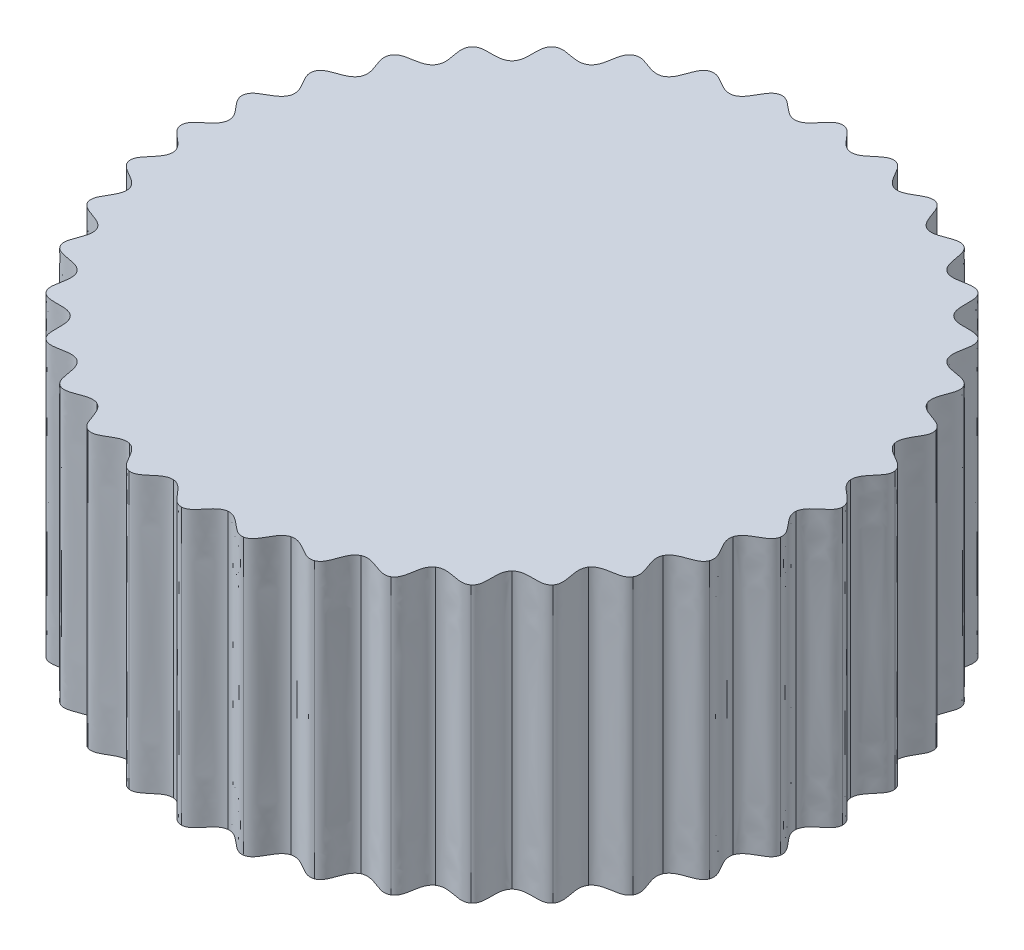
SolidWorks part; units mm, degrees
ref_plane "Front Plane" through (0, 0, 0) normal (0, 0, 1) x (1, 0, 0)
ref_plane "Top Plane" through (0, 0, 0) normal (0, 1, 0) x (1, 0, 0)
ref_plane "Right Plane" through (0, 0, 0) normal (1, 0, 0) x (0, 0, -1)
sketch "Sketch1" plane through (0, 0, 0) normal (0, 1, 0) x (1, 0, 0)
  line L0 (0, 0) -> (0, 36) construction
  line L1 (0, 0) -> (3.1376, 35.863) construction
  line L2 (-0.5, 36) -> (0.5, 36) construction
  line L4 (0, 36) -> (2.9633, 33.8706) construction
  circle A1 centre (0, 0) radius 36 construction
  circle A2 centre (0, 0) radius 34 construction
  spline S0 degree 3 poles (0, 36) (0.6252, 36.0076) (1.4819, 34.8993) (2.3376, 33.935) (2.9633, 33.8706) knots 0 0 0 0 0.5 1 1 1 1
  spline S1 degree 3 poles (0, 36) (-0.6252, 36.0076) (-1.4819, 34.8993) (-2.3376, 33.935) (-2.9633, 33.8706) knots 0 0 0 0 0.5 1 1 1 1
  spline S2 degree 3 poles (6.2513, 35.4531) (5.6369, 35.5691) (4.6008, 34.6264) (3.5907, 33.8254) (2.9633, 33.8706) knots 0 0 0 0 0.5 1 1 1 1
  spline S3 degree 3 poles (6.2513, 35.4531) (6.8684, 35.3519) (7.5196, 34.1118) (8.1948, 33.0136) (8.7998, 32.8415) knots 0 0 0 0 0.5 1 1 1 1
  spline S4 degree 3 poles (12.3127, 33.8289) (11.7278, 34.0499) (10.5438, 33.3015) (9.4099, 32.688) (8.7998, 32.8415) knots 0 0 0 0 0.5 1 1 1 1
  spline S5 degree 3 poles (12.3127, 33.8289) (12.9028, 33.6222) (13.3288, 32.2878) (13.8031, 31.089) (14.369, 30.8145) knots 0 0 0 0 0.5 1 1 1 1
  spline S6 degree 3 poles (18, 31.1769) (17.4623, 31.4961) (16.1663, 30.9646) (14.9431, 30.5574) (14.369, 30.8145) knots 0 0 0 0 0.5 1 1 1 1
  spline S7 degree 3 poles (18, 31.1769) (18.5452, 30.8708) (18.733, 29.4828) (18.9919, 28.2198) (19.5016, 27.8512) knots 0 0 0 0 0.5 1 1 1 1
  spline S8 degree 3 poles (23.1404, 27.5776) (22.6663, 27.9853) (21.2977, 27.687) (20.0223, 27.4983) (19.5016, 27.8512) knots 0 0 0 0 0.5 1 1 1 1
  spline S9 degree 3 poles (23.1404, 27.5776) (23.6242, 27.1815) (23.568, 25.7819) (23.6037, 24.4932) (24.0416, 24.0416) knots 0 0 0 0 0.5 1 1 1 1
  spline S10 degree 3 poles (27.5776, 23.1404) (27.1815, 23.6242) (25.7819, 23.568) (24.4932, 23.6037) (24.0416, 24.0416) knots 0 0 0 0 0.5 1 1 1 1
  spline S11 degree 3 poles (27.5776, 23.1404) (27.9853, 22.6663) (27.687, 21.2977) (27.4983, 20.0223) (27.8512, 19.5016) knots 0 0 0 0 0.5 1 1 1 1
  spline S12 degree 3 poles (31.1769, 18) (30.8708, 18.5452) (29.4828, 18.733) (28.2198, 18.9919) (27.8512, 19.5016) knots 0 0 0 0 0.5 1 1 1 1
  spline S13 degree 3 poles (31.1769, 18) (31.4961, 17.4623) (30.9646, 16.1663) (30.5574, 14.9431) (30.8145, 14.369) knots 0 0 0 0 0.5 1 1 1 1
  spline S14 degree 3 poles (33.8289, 12.3127) (33.6222, 12.9028) (32.2878, 13.3288) (31.089, 13.8031) (30.8145, 14.369) knots 0 0 0 0 0.5 1 1 1 1
  spline S15 degree 3 poles (33.8289, 12.3127) (34.0499, 11.7278) (33.3015, 10.5438) (32.688, 9.4099) (32.8415, 8.7998) knots 0 0 0 0 0.5 1 1 1 1
  spline S16 degree 3 poles (35.4531, 6.2513) (35.3519, 6.8684) (34.1118, 7.5196) (33.0136, 8.1948) (32.8415, 8.7998) knots 0 0 0 0 0.5 1 1 1 1
  spline S17 degree 3 poles (35.4531, 6.2513) (35.5691, 5.6369) (34.6264, 4.6008) (33.8254, 3.5907) (33.8706, 2.9633) knots 0 0 0 0 0.5 1 1 1 1
  spline S18 degree 3 poles (36, 0) (36.0076, 0.6252) (34.8993, 1.4819) (33.935, 2.3376) (33.8706, 2.9633) knots 0 0 0 0 0.5 1 1 1 1
  spline S19 degree 3 poles (36, 0) (36.0076, -0.6252) (34.8993, -1.4819) (33.935, -2.3376) (33.8706, -2.9633) knots 0 0 0 0 0.5 1 1 1 1
  spline S20 degree 3 poles (35.4531, -6.2513) (35.5691, -5.6369) (34.6264, -4.6008) (33.8254, -3.5907) (33.8706, -2.9633) knots 0 0 0 0 0.5 1 1 1 1
  spline S21 degree 3 poles (35.4531, -6.2513) (35.3519, -6.8684) (34.1118, -7.5196) (33.0136, -8.1948) (32.8415, -8.7998) knots 0 0 0 0 0.5 1 1 1 1
  spline S22 degree 3 poles (33.8289, -12.3127) (34.0499, -11.7278) (33.3015, -10.5438) (32.688, -9.4099) (32.8415, -8.7998) knots 0 0 0 0 0.5 1 1 1 1
  spline S23 degree 3 poles (33.8289, -12.3127) (33.6222, -12.9028) (32.2878, -13.3288) (31.089, -13.8031) (30.8145, -14.369) knots 0 0 0 0 0.5 1 1 1 1
  spline S24 degree 3 poles (31.1769, -18) (31.4961, -17.4623) (30.9646, -16.1663) (30.5574, -14.9431) (30.8145, -14.369) knots 0 0 0 0 0.5 1 1 1 1
  spline S25 degree 3 poles (31.1769, -18) (30.8708, -18.5452) (29.4828, -18.733) (28.2198, -18.9919) (27.8512, -19.5016) knots 0 0 0 0 0.5 1 1 1 1
  spline S26 degree 3 poles (27.5776, -23.1404) (27.9853, -22.6663) (27.687, -21.2977) (27.4983, -20.0223) (27.8512, -19.5016) knots 0 0 0 0 0.5 1 1 1 1
  spline S27 degree 3 poles (27.5776, -23.1404) (27.1815, -23.6242) (25.7819, -23.568) (24.4932, -23.6037) (24.0416, -24.0416) knots 0 0 0 0 0.5 1 1 1 1
  spline S28 degree 3 poles (23.1404, -27.5776) (23.6242, -27.1815) (23.568, -25.7819) (23.6037, -24.4932) (24.0416, -24.0416) knots 0 0 0 0 0.5 1 1 1 1
  spline S29 degree 3 poles (23.1404, -27.5776) (22.6663, -27.9853) (21.2977, -27.687) (20.0223, -27.4983) (19.5016, -27.8512) knots 0 0 0 0 0.5 1 1 1 1
  spline S30 degree 3 poles (18, -31.1769) (18.5452, -30.8708) (18.733, -29.4828) (18.9919, -28.2198) (19.5016, -27.8512) knots 0 0 0 0 0.5 1 1 1 1
  spline S31 degree 3 poles (18, -31.1769) (17.4623, -31.4961) (16.1663, -30.9646) (14.9431, -30.5574) (14.369, -30.8145) knots 0 0 0 0 0.5 1 1 1 1
  spline S32 degree 3 poles (12.3127, -33.8289) (12.9028, -33.6222) (13.3288, -32.2878) (13.8031, -31.089) (14.369, -30.8145) knots 0 0 0 0 0.5 1 1 1 1
  spline S33 degree 3 poles (12.3127, -33.8289) (11.7278, -34.0499) (10.5438, -33.3015) (9.4099, -32.688) (8.7998, -32.8415) knots 0 0 0 0 0.5 1 1 1 1
  spline S34 degree 3 poles (6.2513, -35.4531) (6.8684, -35.3519) (7.5196, -34.1118) (8.1948, -33.0136) (8.7998, -32.8415) knots 0 0 0 0 0.5 1 1 1 1
  spline S35 degree 3 poles (6.2513, -35.4531) (5.6369, -35.5691) (4.6008, -34.6264) (3.5907, -33.8254) (2.9633, -33.8706) knots 0 0 0 0 0.5 1 1 1 1
  spline S36 degree 3 poles (0, -36) (0.6252, -36.0076) (1.4819, -34.8993) (2.3376, -33.935) (2.9633, -33.8706) knots 0 0 0 0 0.5 1 1 1 1
  spline S37 degree 3 poles (0, -36) (-0.6252, -36.0076) (-1.4819, -34.8993) (-2.3376, -33.935) (-2.9633, -33.8706) knots 0 0 0 0 0.5 1 1 1 1
  spline S38 degree 3 poles (-6.2513, -35.4531) (-5.6369, -35.5691) (-4.6008, -34.6264) (-3.5907, -33.8254) (-2.9633, -33.8706) knots 0 0 0 0 0.5 1 1 1 1
  spline S39 degree 3 poles (-6.2513, -35.4531) (-6.8684, -35.3519) (-7.5196, -34.1118) (-8.1948, -33.0136) (-8.7998, -32.8415) knots 0 0 0 0 0.5 1 1 1 1
  spline S40 degree 3 poles (-12.3127, -33.8289) (-11.7278, -34.0499) (-10.5438, -33.3015) (-9.4099, -32.688) (-8.7998, -32.8415) knots 0 0 0 0 0.5 1 1 1 1
  spline S41 degree 3 poles (-12.3127, -33.8289) (-12.9028, -33.6222) (-13.3288, -32.2878) (-13.8031, -31.089) (-14.369, -30.8145) knots 0 0 0 0 0.5 1 1 1 1
  spline S42 degree 3 poles (-18, -31.1769) (-17.4623, -31.4961) (-16.1663, -30.9646) (-14.9431, -30.5574) (-14.369, -30.8145) knots 0 0 0 0 0.5 1 1 1 1
  spline S43 degree 3 poles (-18, -31.1769) (-18.5452, -30.8708) (-18.733, -29.4828) (-18.9919, -28.2198) (-19.5016, -27.8512) knots 0 0 0 0 0.5 1 1 1 1
  spline S44 degree 3 poles (-23.1404, -27.5776) (-22.6663, -27.9853) (-21.2977, -27.687) (-20.0223, -27.4983) (-19.5016, -27.8512) knots 0 0 0 0 0.5 1 1 1 1
  spline S45 degree 3 poles (-23.1404, -27.5776) (-23.6242, -27.1815) (-23.568, -25.7819) (-23.6037, -24.4932) (-24.0416, -24.0416) knots 0 0 0 0 0.5 1 1 1 1
  spline S46 degree 3 poles (-27.5776, -23.1404) (-27.1815, -23.6242) (-25.7819, -23.568) (-24.4932, -23.6037) (-24.0416, -24.0416) knots 0 0 0 0 0.5 1 1 1 1
  spline S47 degree 3 poles (-27.5776, -23.1404) (-27.9853, -22.6663) (-27.687, -21.2977) (-27.4983, -20.0223) (-27.8512, -19.5016) knots 0 0 0 0 0.5 1 1 1 1
  spline S48 degree 3 poles (-31.1769, -18) (-30.8708, -18.5452) (-29.4828, -18.733) (-28.2198, -18.9919) (-27.8512, -19.5016) knots 0 0 0 0 0.5 1 1 1 1
  spline S49 degree 3 poles (-31.1769, -18) (-31.4961, -17.4623) (-30.9646, -16.1663) (-30.5574, -14.9431) (-30.8145, -14.369) knots 0 0 0 0 0.5 1 1 1 1
  spline S50 degree 3 poles (-33.8289, -12.3127) (-33.6222, -12.9028) (-32.2878, -13.3288) (-31.089, -13.8031) (-30.8145, -14.369) knots 0 0 0 0 0.5 1 1 1 1
  spline S51 degree 3 poles (-33.8289, -12.3127) (-34.0499, -11.7278) (-33.3015, -10.5438) (-32.688, -9.4099) (-32.8415, -8.7998) knots 0 0 0 0 0.5 1 1 1 1
  spline S52 degree 3 poles (-35.4531, -6.2513) (-35.3519, -6.8684) (-34.1118, -7.5196) (-33.0136, -8.1948) (-32.8415, -8.7998) knots 0 0 0 0 0.5 1 1 1 1
  spline S53 degree 3 poles (-35.4531, -6.2513) (-35.5691, -5.6369) (-34.6264, -4.6008) (-33.8254, -3.5907) (-33.8706, -2.9633) knots 0 0 0 0 0.5 1 1 1 1
  spline S54 degree 3 poles (-36, 0) (-36.0076, -0.6252) (-34.8993, -1.4819) (-33.935, -2.3376) (-33.8706, -2.9633) knots 0 0 0 0 0.5 1 1 1 1
  spline S55 degree 3 poles (-36, 0) (-36.0076, 0.6252) (-34.8993, 1.4819) (-33.935, 2.3376) (-33.8706, 2.9633) knots 0 0 0 0 0.5 1 1 1 1
  spline S56 degree 3 poles (-35.4531, 6.2513) (-35.5691, 5.6369) (-34.6264, 4.6008) (-33.8254, 3.5907) (-33.8706, 2.9633) knots 0 0 0 0 0.5 1 1 1 1
  spline S57 degree 3 poles (-35.4531, 6.2513) (-35.3519, 6.8684) (-34.1118, 7.5196) (-33.0136, 8.1948) (-32.8415, 8.7998) knots 0 0 0 0 0.5 1 1 1 1
  spline S58 degree 3 poles (-33.8289, 12.3127) (-34.0499, 11.7278) (-33.3015, 10.5438) (-32.688, 9.4099) (-32.8415, 8.7998) knots 0 0 0 0 0.5 1 1 1 1
  spline S59 degree 3 poles (-33.8289, 12.3127) (-33.6222, 12.9028) (-32.2878, 13.3288) (-31.089, 13.8031) (-30.8145, 14.369) knots 0 0 0 0 0.5 1 1 1 1
  spline S60 degree 3 poles (-31.1769, 18) (-31.4961, 17.4623) (-30.9646, 16.1663) (-30.5574, 14.9431) (-30.8145, 14.369) knots 0 0 0 0 0.5 1 1 1 1
  spline S61 degree 3 poles (-31.1769, 18) (-30.8708, 18.5452) (-29.4828, 18.733) (-28.2198, 18.9919) (-27.8512, 19.5016) knots 0 0 0 0 0.5 1 1 1 1
  spline S62 degree 3 poles (-27.5776, 23.1404) (-27.9853, 22.6663) (-27.687, 21.2977) (-27.4983, 20.0223) (-27.8512, 19.5016) knots 0 0 0 0 0.5 1 1 1 1
  spline S63 degree 3 poles (-27.5776, 23.1404) (-27.1815, 23.6242) (-25.7819, 23.568) (-24.4932, 23.6037) (-24.0416, 24.0416) knots 0 0 0 0 0.5 1 1 1 1
  spline S64 degree 3 poles (-23.1404, 27.5776) (-23.6242, 27.1815) (-23.568, 25.7819) (-23.6037, 24.4932) (-24.0416, 24.0416) knots 0 0 0 0 0.5 1 1 1 1
  spline S65 degree 3 poles (-23.1404, 27.5776) (-22.6663, 27.9853) (-21.2977, 27.687) (-20.0223, 27.4983) (-19.5016, 27.8512) knots 0 0 0 0 0.5 1 1 1 1
  spline S66 degree 3 poles (-18, 31.1769) (-18.5452, 30.8708) (-18.733, 29.4828) (-18.9919, 28.2198) (-19.5016, 27.8512) knots 0 0 0 0 0.5 1 1 1 1
  spline S67 degree 3 poles (-18, 31.1769) (-17.4623, 31.4961) (-16.1663, 30.9646) (-14.9431, 30.5574) (-14.369, 30.8145) knots 0 0 0 0 0.5 1 1 1 1
  spline S68 degree 3 poles (-12.3127, 33.8289) (-12.9028, 33.6222) (-13.3288, 32.2878) (-13.8031, 31.089) (-14.369, 30.8145) knots 0 0 0 0 0.5 1 1 1 1
  spline S69 degree 3 poles (-12.3127, 33.8289) (-11.7278, 34.0499) (-10.5438, 33.3015) (-9.4099, 32.688) (-8.7998, 32.8415) knots 0 0 0 0 0.5 1 1 1 1
  spline S70 degree 3 poles (-6.2513, 35.4531) (-6.8684, 35.3519) (-7.5196, 34.1118) (-8.1948, 33.0136) (-8.7998, 32.8415) knots 0 0 0 0 0.5 1 1 1 1
  spline S71 degree 3 poles (-6.2513, 35.4531) (-5.6369, 35.5691) (-4.6008, 34.6264) (-3.5907, 33.8254) (-2.9633, 33.8706) knots 0 0 0 0 0.5 1 1 1 1
  point P190 (0, 0)
  dimension "D1" = 72
  dimension "D3" = 5
  dimension "D6" = 2
  dimension "D5" = 1
extrude "Boss-Extrude1" add sketch "Sketch1" along normal blind 30
